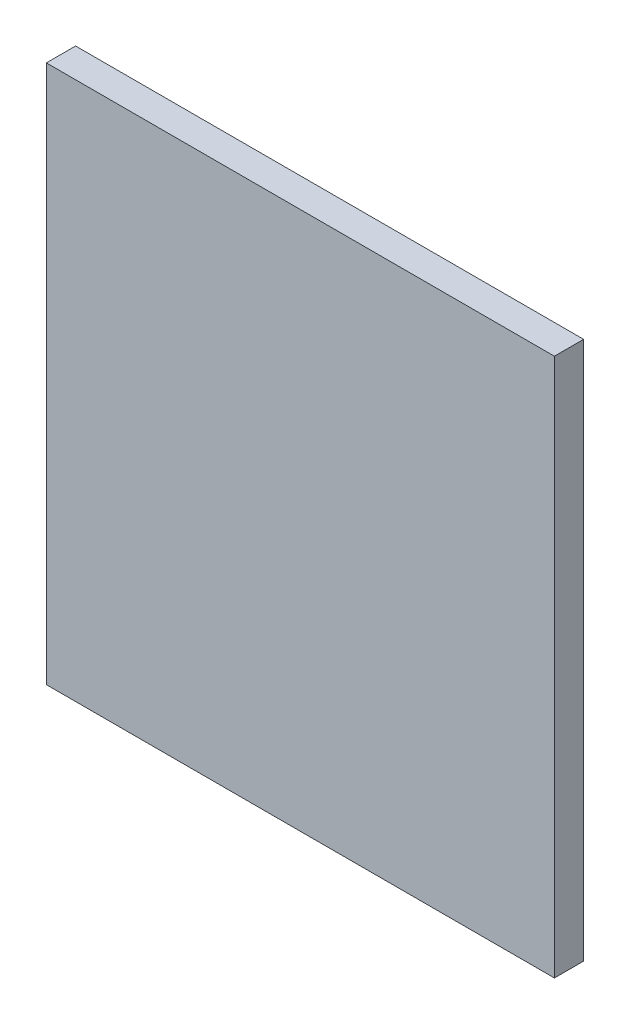
SolidWorks part; units mm, degrees
material "ABS PC"
ref_plane "Front Plane" through (0, 0, 0) normal (0, 0, 1) x (1, 0, 0)
ref_plane "Top Plane" through (0, 0, 0) normal (0, 1, 0) x (1, 0, 0)
ref_plane "Right Plane" through (0, 0, 0) normal (1, 0, 0) x (0, 0, -1)
sketch "Sketch1" plane through (0, 0, 0) normal (0, 0, 1) x (1, 0, 0)
  line L4 (-67.04, -91.3291) -> (-67.04, -77.2954)
  line L5 (-67.04, -77.2954) -> (-80.28, -77.2954)
  line L6 (-80.28, -77.2954) -> (-80.28, -91.3291)
  line L7 (-80.28, -91.3291) -> (-67.04, -91.3291)
  line L8 (-67.04, -91.3291) -> (-67.04, -77.2954)
  line L9 (-67.04, -77.2954) -> (-80.28, -77.2954)
  line L10 (-80.28, -77.2954) -> (-80.28, -91.3291)
  line L11 (-80.28, -91.3291) -> (-67.04, -91.3291)
  dimension "D1" = 0
extrude "Boss-Extrude1" add sketch "Sketch1" along normal blind 0.762
